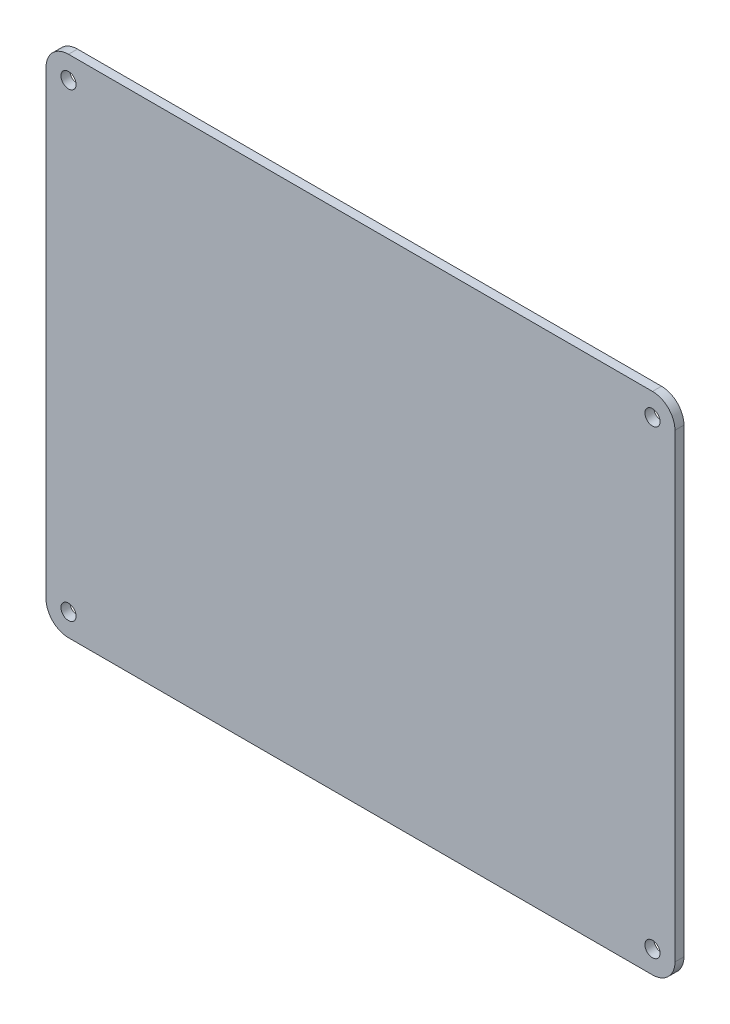
SolidWorks part; units mm, degrees
ref_plane "Front Plane" through (0, 0, 0) normal (0, 0, 1) x (1, 0, 0)
ref_plane "Top Plane" through (0, 0, 0) normal (0, 1, 0) x (1, 0, 0)
ref_plane "Right Plane" through (0, 0, 0) normal (1, 0, 0) x (0, 0, -1)
sketch "Sketch1" plane through (0, 0, 0) normal (0, 0, 1) x (1, 0, 0)
  line L1 (-52, -45) -> (52, -45)
  line L2 (-56, -41) -> (-56, 41)
  line L3 (-52, 45) -> (52, 45)
  line L4 (56, -41) -> (56, 41)
  line L5 (-56, -45) -> (56, 45) construction
  line L6 (-56, 45) -> (56, -45) construction
  arc A0 (-56, -41) -> (-52, -45) centre (-52, -41) ccw
  arc A1 (52, -45) -> (56, -41) centre (52, -41) ccw
  arc A2 (56, 41) -> (52, 45) centre (52, 41) ccw
  arc A3 (-56, 41) -> (-52, 45) centre (-52, 41) cw
  circle A4 centre (-52, 41) radius 1.35
  circle A5 centre (52, 41) radius 1.35
  circle A6 centre (52, -41) radius 1.35
  circle A7 centre (-52, -41) radius 1.35
  point P0 (0, 0)
  dimension "D3" = 4
  dimension "D4" = 2.7
  dimension "D1" = 90
  dimension "D2" = 112
extrude "Boss-Extrude1" add sketch "Sketch1" along normal blind 1.6
